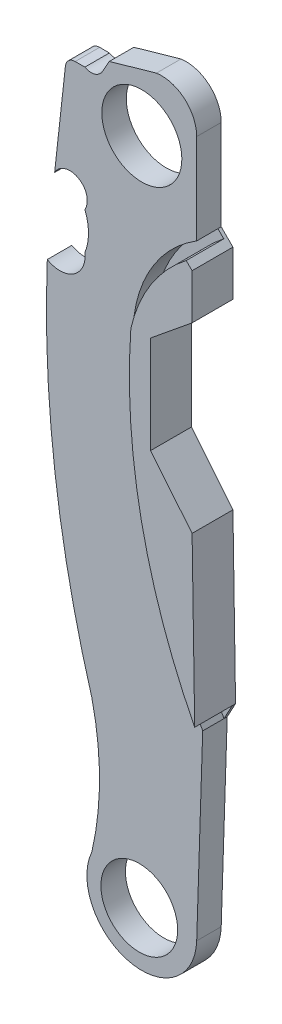
SolidWorks part; units mm, degrees
ref_plane "Front Plane" through (0, 0, 0) normal (0, 0, 1) x (1, 0, 0)
ref_plane "Top Plane" through (0, 0, 0) normal (0, 1, 0) x (1, 0, 0)
ref_plane "Right Plane" through (0, 0, 0) normal (1, 0, 0) x (0, 0, -1)
sketch "Sketch1" plane through (0, 0, 0) normal (0, 0, 1) x (1, 0, 0)
  line L0 (19.4532, 43.7696) -> (97.2658, 43.7696) construction
  line L1 (61.1714, 26.3322) -> (60.7049, 11.9662)
  line L2 (61.1714, 26.3322) -> (61.8192, 27.5333)
  line L3 (61.8192, 27.5333) -> (61.617, 40.4868)
  line L4 (61.617, 40.4868) -> (58.39, 44.4456)
  line L5 (58.39, 44.4456) -> (58.39, 52.0255)
  line L6 (58.39, 52.0255) -> (61.617, 54.656)
  line L7 (61.617, 58.1695) -> (61.617, 54.656)
  line L8 (61.617, 58.1695) -> (60.7049, 59.0816)
  line L9 (60.7049, 59.0816) -> (60.7049, 66.1081)
  line L10 (57.5746, 68.8131) -> (53.9095, 67.7689)
  line L11 (53.9095, 67.7689) -> (53.3739, 66.8212)
  line L12 (52.0128, 66.4383) -> (50.5748, 66.4383)
  line L13 (50.5748, 66.4383) -> (49.6618, 58.1695)
  arc A0 (49.0909, 52.0255) -> (52.552, 24.2699) centre (135.0062, 48.6454) ccw
  arc A1 (52.552, 24.2699) -> (52.552, 13.8668) centre (30.2387, 19.0683) cw
  arc A2 (52.552, 13.8668) -> (60.7049, 11.9662) centre (56.4387, 12.1024) ccw
  arc A3 (60.7049, 66.1081) -> (57.5746, 68.8131) centre (57.971, 66.1081) ccw
  arc A4 (53.3739, 66.8212) -> (52.0128, 66.4383) centre (52.5006, 67.3148) cw
  arc A5 (49.6618, 58.1695) -> (52.0128, 56.8531) centre (50.8511, 57.5359) cw
  arc A6 (49.0909, 52.0255) -> (52.0128, 53.9491) centre (50.0723, 53.7158) ccw
  arc A7 (52.0128, 56.8531) -> (52.0128, 53.9491) centre (48.4011, 55.4011) cw
  circle A8 centre (56.4387, 64.0208) radius 3.1115
  circle A9 centre (56.242, 11.9572) radius 2.9845
  dimension "D1" = 5.969
  dimension "D2" = 6.223
  dimension "D3" = 2.7339
  dimension "D11" = 4.2684
  dimension "D12" = 22.9116
  dimension "D13" = 85.9817
  dimension "D15" = 1.3475
  dimension "D16" = 3.8927
  dimension "D17" = 1.9545
  dimension "D4" = 3.5135
  dimension "D5" = 7.0265
  dimension "D6" = 4.1633
  dimension "D7" = 7.58
  dimension "D8" = 5.1074
  dimension "D9" = 12.9535
  dimension "D10" = 14.366
  dimension "D14" = 8.319
extrude "Boss-Extrude1" add sketch "Sketch1" along normal blind 1.905
sketch "Sketch2" plane through (0, 0, 1.905) normal (0, 0, 1) x (1, 0, 0)
  line L0 (672, 1512) -> (3360, 1512) construction
  line L3 (60.7049, 59.0816) -> (61.161, 58.6256)
  line L4 (61.8192, 27.5333) -> (61.1714, 26.3322)
  arc A0 (56.8556, 51.9014) -> (61.8192, 27.5333) centre (103.0956, 48.6305) ccw
  arc A1 (56.8556, 51.9014) -> (61.161, 58.6256) centre (68.294, 49.3181) cw
  arc A2 (55.8335, 51.58) -> (61.1714, 26.3322) centre (101.722, 48.0936) ccw
  arc A3 (55.8335, 51.58) -> (60.7049, 59.0816) centre (66.1632, 50.2045) cw
  dimension "D1" = 46.3555
  dimension "D2" = 11.7265
  dimension "D3" = 10.4209
  dimension "D4" = 46.0208
extrude "Cut-Extrude1" cut sketch "Sketch2" against normal blind 1.651
sketch "Sketch3" plane through (0, 0, 1.905) normal (0, 0, 1) x (1, 0, 0)
  line L6 (61.8192, 27.5333) -> (61.617, 40.4868)
  line L7 (61.617, 40.4868) -> (58.39, 44.4456)
  line L8 (58.39, 44.4456) -> (58.39, 52.0255)
  line L9 (58.39, 52.0255) -> (61.617, 54.656)
  line L10 (61.617, 54.656) -> (61.617, 58.1695)
  line L11 (61.617, 58.1695) -> (61.161, 58.6256)
  line L12 (61.8192, 27.5333) -> (61.617, 40.4868)
  line L13 (61.617, 40.4868) -> (58.39, 44.4456)
  line L14 (58.39, 44.4456) -> (58.39, 52.0255)
  line L15 (58.39, 52.0255) -> (61.617, 54.656)
  line L16 (61.617, 54.656) -> (61.617, 58.1695)
  line L17 (61.617, 58.1695) -> (61.161, 58.6256)
  arc A2 (61.161, 58.6256) -> (56.8556, 51.9014) centre (68.294, 49.3181) ccw
  arc A3 (56.8556, 51.9014) -> (61.8192, 27.5333) centre (103.0956, 48.6305) ccw
  arc A4 (61.161, 58.6256) -> (56.8556, 51.9014) centre (68.294, 49.3181) ccw
  arc A5 (56.8556, 51.9014) -> (61.8192, 27.5333) centre (103.0956, 48.6305) ccw
  dimension "D1" = 0
extrude "Boss-Extrude2" add sketch "Sketch3" along normal blind 1.27
fillet "Fillet4" radius 0.762 1 edges at (50.5748, 66.4383, 0.9525)
